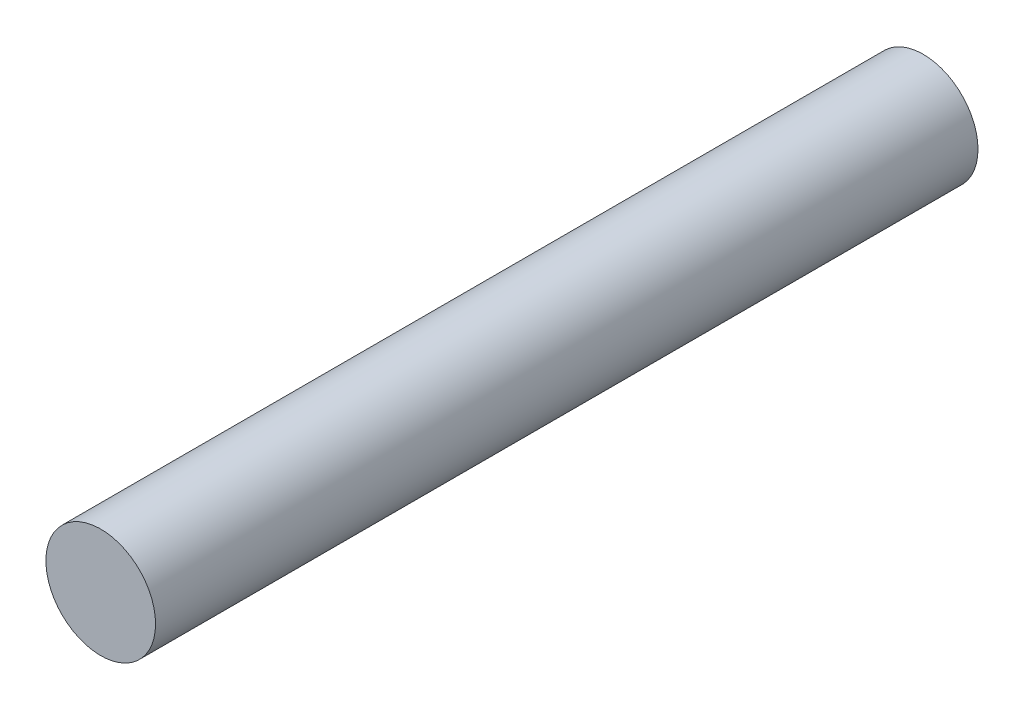
SolidWorks part; units mm, degrees
material "6061 Alloy"
ref_plane "Front Plane" through (0, 0, 0) normal (0, 0, 1) x (1, 0, 0)
ref_plane "Top Plane" through (0, 0, 0) normal (0, 1, 0) x (1, 0, 0)
ref_plane "Right Plane" through (0, 0, 0) normal (1, 0, 0) x (0, 0, -1)
sketch "Sketch1" plane through (0, 0, 0) normal (0, 0, 1) x (1, 0, 0)
  circle A0 centre (0, 0) radius 4
extrude "Boss-Extrude1" add sketch "Sketch1" along normal blind 60
